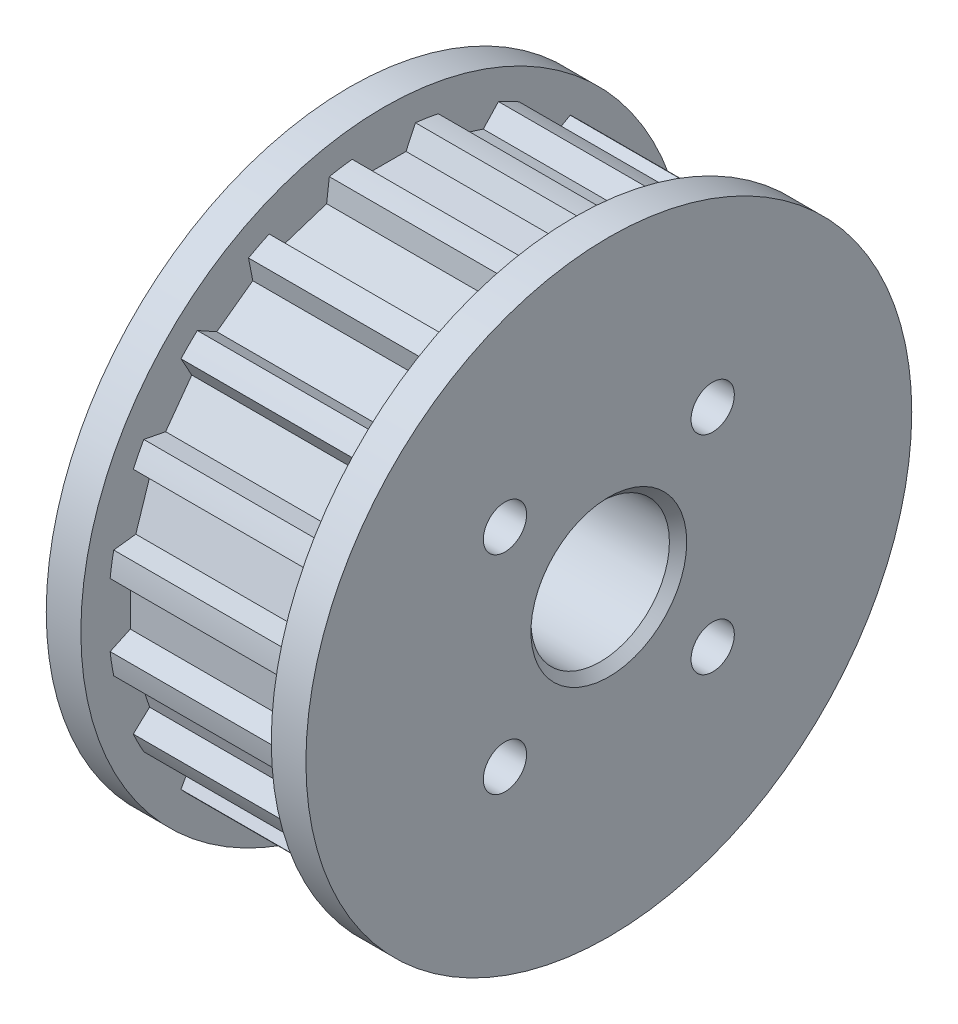
SolidWorks part; units mm, degrees
material "6061 合金"
ref_plane "前视基准面" through (0, 0, 0) normal (0, 0, 1) x (1, 0, 0)
ref_plane "上视基准面" through (0, 0, 0) normal (0, 1, 0) x (1, 0, 0)
ref_plane "右视基准面" through (0, 0, 0) normal (1, 0, 0) x (0, 0, -1)
sketch "草图1" plane through (0, 0, 0) normal (1, 0, 0) x (0, 0, -1)
  line L0 (0, 0) -> (0, 19.2746) construction
  line L1 (-1.285, 14.645) -> (1.285, 14.645)
  line L2 (1.285, 14.645) -> (1.8281, 15.8097)
  line L3 (3.3034, 14.3253) -> (5.7477, 13.5311)
  line L4 (5.7477, 13.5311) -> (6.6241, 14.471)
  line L5 (3.3034, 14.3253) -> (3.1468, 15.6008)
  line L6 (7.5685, 12.6034) -> (9.6477, 11.0927)
  line L7 (9.6477, 11.0927) -> (10.7716, 11.7158)
  line L8 (7.5685, 12.6034) -> (7.8137, 13.8648)
  line L9 (11.0927, 9.6477) -> (12.6034, 7.5685)
  line L10 (12.6034, 7.5685) -> (13.8648, 7.8137)
  line L11 (11.0927, 9.6477) -> (11.7158, 10.7716)
  line L12 (13.5311, 5.7477) -> (14.3253, 3.3034)
  line L13 (14.3253, 3.3034) -> (15.6008, 3.1468)
  line L14 (13.5311, 5.7477) -> (14.471, 6.6241)
  line L15 (14.645, 1.285) -> (14.645, -1.285)
  line L16 (14.645, -1.285) -> (15.8097, -1.8281)
  line L17 (14.645, 1.285) -> (15.8097, 1.8281)
  line L18 (14.3253, -3.3034) -> (13.5311, -5.7477)
  line L19 (13.5311, -5.7477) -> (14.471, -6.6241)
  line L20 (14.3253, -3.3034) -> (15.6008, -3.1468)
  line L21 (12.6034, -7.5685) -> (11.0927, -9.6477)
  line L22 (0, 0) -> (3.8627, 24.3882) construction
  line L23 (11.0927, -9.6477) -> (11.7158, -10.7716)
  line L24 (-1.285, 14.645) -> (-1.8281, 15.8097)
  line L25 (12.6034, -7.5685) -> (13.8648, -7.8137)
  line L26 (9.6477, -11.0927) -> (7.5685, -12.6034)
  line L27 (7.5685, -12.6034) -> (7.8137, -13.8648)
  line L28 (9.6477, -11.0927) -> (10.7716, -11.7158)
  line L29 (5.7477, -13.5311) -> (3.3034, -14.3253)
  line L30 (3.3034, -14.3253) -> (3.1468, -15.6008)
  line L31 (5.7477, -13.5311) -> (6.6241, -14.471)
  line L32 (1.285, -14.645) -> (-1.285, -14.645)
  line L33 (-1.285, -14.645) -> (-1.8281, -15.8097)
  line L34 (1.285, -14.645) -> (1.8281, -15.8097)
  line L35 (-3.3034, -14.3253) -> (-5.7477, -13.5311)
  line L36 (-5.7477, -13.5311) -> (-6.6241, -14.471)
  line L37 (-3.3034, -14.3253) -> (-3.1468, -15.6008)
  line L38 (-7.5685, -12.6034) -> (-9.6477, -11.0927)
  line L39 (-9.6477, -11.0927) -> (-10.7716, -11.7158)
  line L40 (-7.5685, -12.6034) -> (-7.8137, -13.8648)
  line L41 (-11.0927, -9.6477) -> (-12.6034, -7.5685)
  line L42 (-12.6034, -7.5685) -> (-13.8648, -7.8137)
  line L43 (-11.0927, -9.6477) -> (-11.7158, -10.7716)
  line L44 (-13.5311, -5.7477) -> (-14.3253, -3.3034)
  line L45 (-14.3253, -3.3034) -> (-15.6008, -3.1468)
  line L46 (-13.5311, -5.7477) -> (-14.471, -6.6241)
  line L47 (-14.645, -1.285) -> (-14.645, 1.285)
  line L48 (-14.645, 1.285) -> (-15.8097, 1.8281)
  line L49 (-14.645, -1.285) -> (-15.8097, -1.8281)
  line L50 (-14.3253, 3.3034) -> (-13.5311, 5.7477)
  line L51 (-13.5311, 5.7477) -> (-14.471, 6.6241)
  line L52 (-14.3253, 3.3034) -> (-15.6008, 3.1468)
  line L53 (-12.6034, 7.5685) -> (-11.0927, 9.6477)
  line L54 (-11.0927, 9.6477) -> (-11.7158, 10.7716)
  line L55 (-12.6034, 7.5685) -> (-13.8648, 7.8137)
  line L56 (-9.6477, 11.0927) -> (-7.5685, 12.6034)
  line L57 (-7.5685, 12.6034) -> (-7.8137, 13.8648)
  line L58 (-9.6477, 11.0927) -> (-10.7716, 11.7158)
  line L59 (-5.7477, 13.5311) -> (-3.3034, 14.3253)
  line L60 (-3.3034, 14.3253) -> (-3.1468, 15.6008)
  line L61 (-5.7477, 13.5311) -> (-6.6241, 14.471)
  arc A0 (-1.8281, 15.8097) -> (-3.1468, 15.6008) centre (0, 0) ccw
  circle A1 centre (0, 0) radius 4
  arc A2 (-6.6241, 14.471) -> (-7.8137, 13.8648) centre (0, 0) ccw
  arc A3 (3.1468, 15.6008) -> (1.8281, 15.8097) centre (0, 0) ccw
  arc A4 (7.8137, 13.8648) -> (6.6241, 14.471) centre (0, 0) ccw
  arc A5 (11.7158, 10.7716) -> (10.7716, 11.7158) centre (0, 0) ccw
  arc A6 (14.471, 6.6241) -> (13.8648, 7.8137) centre (0, 0) ccw
  arc A7 (15.8097, 1.8281) -> (15.6008, 3.1468) centre (0, 0) ccw
  arc A8 (15.6008, -3.1468) -> (15.8097, -1.8281) centre (0, 0) ccw
  arc A9 (13.8648, -7.8137) -> (14.471, -6.6241) centre (0, 0) ccw
  arc A10 (10.7716, -11.7158) -> (11.7158, -10.7716) centre (0, 0) ccw
  arc A11 (6.6241, -14.471) -> (7.8137, -13.8648) centre (0, 0) ccw
  arc A12 (1.8281, -15.8097) -> (3.1468, -15.6008) centre (0, 0) ccw
  arc A13 (-3.1468, -15.6008) -> (-1.8281, -15.8097) centre (0, 0) ccw
  arc A14 (-7.8137, -13.8648) -> (-6.6241, -14.471) centre (0, 0) ccw
  arc A15 (-11.7158, -10.7716) -> (-10.7716, -11.7158) centre (0, 0) ccw
  arc A16 (-14.471, -6.6241) -> (-13.8648, -7.8137) centre (0, 0) ccw
  arc A17 (-15.8097, -1.8281) -> (-15.6008, -3.1468) centre (0, 0) ccw
  arc A18 (-15.6008, 3.1468) -> (-15.8097, 1.8281) centre (0, 0) ccw
  arc A19 (-13.8648, 7.8137) -> (-14.471, 6.6241) centre (0, 0) ccw
  arc A20 (-10.7716, 11.7158) -> (-11.7158, 10.7716) centre (0, 0) ccw
  point P32 (0, 14.645)
  dimension "D1" = 8
  dimension "D2" = 31.83
  dimension "D4" = 9
  dimension "D3" = 1.285
  dimension "D5" = 115
  dimension "D6" = 14.645
  dimension "D7" = 20
extrude "凸台-拉伸1" add sketch "草图1" along normal blind 11 contours L59 L60 A0 L24 L1 L2 A3 L5 L3 L4 A4 L8 L6 L7 A5 L11 L9 L10 A6 L14 L12 L13 A7 L17 L15 L16 A8 L20 L18 L19 A9 L25 L21 L23 A10 L28 L26 L27 A11 L31 L29 L30 A12 L34 L32 L33 A13 L37 L35 L36 A14 L40 L38 L39 A15 L43 L41 L42 A16 L46 L44 L45 A17 L49 L47 L48 A18 L52 L50 L51 A19 L55 L53 L54 A20 L58 L56 L57 A2 L61
sketch "草图2" plane through (11, 0, 0) normal (1, 0, 0) x (0, 0, -1)
  circle A0 centre (0, 0) radius 17.5
  circle A1 centre (0, 0) radius 4
  dimension "D1" = 35
extrude "凸台-拉伸2" add sketch "草图2" along normal blind 2
sketch "草图3" plane through (0, 0, 0) normal (-1, 0, 0) x (0, 0, 1)
  circle A0 centre (0, 0) radius 4
  circle A1 centre (0, 0) radius 17.5
  dimension "D1" = 35
extrude "凸台-拉伸3" add sketch "草图3" along normal blind 2
chamfer "倒角1" distance 0.5 angle 45 2 edges at (13, 0, -4) (-2, 0, 4)
hole_wizard "M3 螺纹孔1" positions "草图6" profile "草图7" tap size "M3" standard "GB"
sketch "草图6" plane through (13, 0, 0) normal (1, 0, 0) x (0, 0, -1)
  line L0 (0, 17.555) -> (0, -21.8154) construction
  line L2 (21.8667, 0) -> (-23.15, 0) construction
  point P0 (-6, 6)
  point P2 (6, 6)
  point P4 (6, -6)
  point P6 (-6, -6)
  dimension "D1" = 6
  dimension "D2" = 6
  dimension "D3" = 6
  dimension "D4" = 6
  dimension "D5" = 6
  dimension "D6" = 6
  dimension "D7" = 6
  dimension "D8" = 6
sketch "草图7" plane through (13, 6, 6) normal (0, 1, 0) x (0, 0, -1)
  line L0 (0, 0) -> (0, 5.7511)
  line L1 (0, 5.7511) -> (1.25, 5)
  line L2 (1.25, 5) -> (1.25, 0)
  line L5 (1.25, 0) -> (0, 0)
  line L10 (0, 5.7511) -> (-1.25, 5) construction
  line L11 (0, -6.35) -> (0, 107.95) construction
  dimension "螺纹孔钻头直径" = 2.5
  dimension "螺纹孔钻头深度" = 5
  dimension "导头角度" = 118
cosmetic thread "孔螺蚊线1" parameters "D1"=4, "D2"=3
cosmetic thread "孔螺蚊线2" parameters "D1"=4, "D2"=3
cosmetic thread "孔螺蚊线3" parameters "D1"=4, "D2"=3
cosmetic thread "孔螺蚊线4" parameters "D1"=4, "D2"=3
hole_wizard "M3 螺纹孔2" positions "草图8" profile "草图9" tap size "M3" standard "GB"
sketch "草图8" plane through (-2, 0, 0) normal (-1, 0, 0) x (0, 0, 1)
  line L0 (-21.1786, 0) -> (22.7536, 0) construction
  line L2 (0, 17.5) -> (0, -19.5799) construction
  circle A0 centre (0, 0) radius 17.5 construction
  point P0 (-6, 6)
  point P18 (-5.9667, 5.7476)
  point P19 (6, 6)
  point P20 (6, -6)
  point P21 (-6, -6)
  dimension "D1" = 6
  dimension "D2" = 6
sketch "草图9" plane through (-2, 6, -6) normal (0, 1, 0) x (0, 0, 1)
  line L0 (0, 0) -> (0, 5.7511)
  line L1 (0, 5.7511) -> (1.25, 5)
  line L2 (1.25, 5) -> (1.25, 0)
  line L5 (1.25, 0) -> (0, 0)
  line L10 (0, 5.7511) -> (-1.25, 5) construction
  line L11 (0, -6.35) -> (0, 107.95) construction
  dimension "螺纹孔钻头直径" = 2.5
  dimension "螺纹孔钻头深度" = 5
  dimension "导头角度" = 118
cosmetic thread "孔螺蚊线5" parameters "D1"=4, "D2"=3
cosmetic thread "孔螺蚊线6" parameters "D1"=4, "D2"=3
cosmetic thread "孔螺蚊线7" parameters "D1"=4, "D2"=3
cosmetic thread "孔螺蚊线8" parameters "D1"=4, "D2"=3
